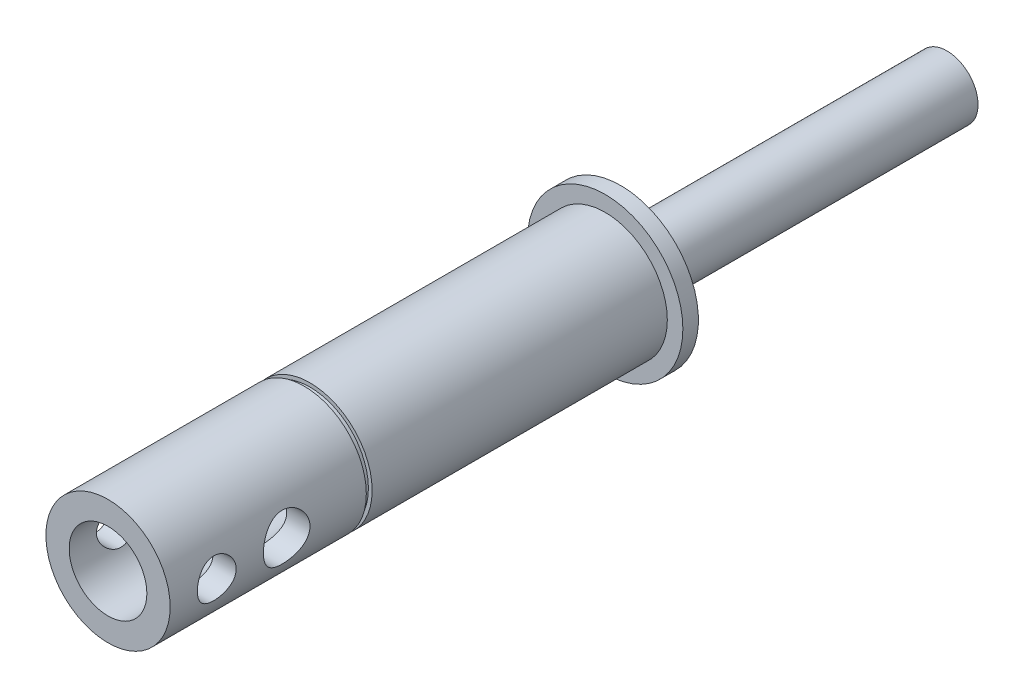
SolidWorks part; units mm, degrees
other "Markup1"
sketch "Sketch20" plane through (-15.875, -15.875, 171.45) normal (-1, 0, 0) x (0, 0, -1)
sketch "Sketch21" plane through (-15.875, -15.875, 171.45) normal (-1, 0, 0) x (0, 0, -1)
material "6061 Alloy"
ref_plane "Front Plane" through (0, 0, 0) normal (0, 0, 1) x (1, 0, 0)
ref_plane "Top Plane" through (0, 0, 0) normal (0, 1, 0) x (1, 0, 0)
ref_plane "Right Plane" through (0, 0, 0) normal (1, 0, 0) x (0, 0, -1)
sketch "Sketch1" plane through (0, 0, 0) normal (0, 0, 1) x (1, 0, 0)
  circle A0 centre (0, 0) radius 15.875
  dimension "D1" = 31.75
extrude "RawStock" add sketch "Sketch1" along normal blind 194.6402
sketch "Sketch10" plane through (0, 0, 194.6402) normal (0, 0, 1) x (1, 0, 0)
  circle A0 centre (0, 0) radius 12.7
extrude "FacingOp" cut sketch "Sketch10" against normal blind 23.1902
hole_wizard "ReliefHole" positions "Sketch2" profile "Sketch3" legacy
sketch "Sketch2" plane through (0, 0, 194.6402) normal (0, 0, 1) x (1, 0, 0)
  point P0 (0, 0)
sketch "Sketch3" plane through (0, 0, 194.6402) normal (1, 0, 0) x (0, -1, 0)
  line L0 (0, 0) -> (0, 95.8905)
  line L1 (0, 95.8905) -> (6.35, 92.075)
  line L2 (6.35, 92.075) -> (6.35, 0)
  line L4 (6.35, 0) -> (0, 0)
  line L6 (0, 95.8905) -> (-6.35, 92.075) construction
  line L7 (0, -4.2442) -> (0, 117.3081) construction
  dimension "Diameter" = 12.7
  dimension "Depth" = 92.075
  dimension "Drill Angle" = 118
hole_wizard "WiresHole" positions "Sketch4" profile "Sketch5" legacy
sketch "Sketch4" plane through (0, 0, 194.6402) normal (0, 0, 1) x (1, 0, 0)
  point P0 (0, 0)
sketch "Sketch5" plane through (0, 0, 194.6402) normal (1, 0, 0) x (0, -1, 0)
  line L0 (0, 0) -> (0, 120.0345)
  line L1 (0, 120.0345) -> (7.9375, 115.2652)
  line L2 (7.9375, 115.2652) -> (7.9375, 0)
  line L4 (7.9375, 0) -> (0, 0)
  line L6 (0, 120.0345) -> (-7.9375, 115.2652) construction
  line L7 (0, -4.2442) -> (0, 117.3081) construction
  dimension "Diameter" = 15.875
  dimension "Depth" = 115.2652
  dimension "Drill Angle" = 118
sketch "Sketch6" plane through (0, 0, 194.6402) normal (0, 0, 1) x (1, 0, 0)
  circle A0 centre (0, 0) radius 12.7
  dimension "D1" = 25.4
extrude "ShaftDiam" cut sketch "Sketch6" against normal blind 124.7902 flip side to cut
ref_plane "GroovePlane" through (0, 0, 130.175) normal (0, 0, 1) x (1, 0, 0)
sketch "Sketch7" plane through (0, 0, 130.175) normal (0, 0, 1) x (1, 0, 0)
  circle A0 centre (0, 0) radius 11.938
  dimension "D1" = 23.876
extrude "Groove" cut sketch "Sketch7" along normal blind 1.1906 flip side to cut
sketch "Sketch8" plane through (0, 0, 0) normal (0, 0, -1) x (-1, 0, 0)
  circle A0 centre (0, 0) radius 6.35
  dimension "D1" = 12.7
extrude "EncoderShaft" cut sketch "Sketch8" against normal blind 66.675 flip side to cut
ref_plane "Plane2" through (-12.7, 0, 0) normal (-1, 0, 0) x (0, 1, 0)
sketch "Sketch12" plane through (-12.7, 0, 0) normal (-1, 0, 0) x (0, 1, 0)
  line L0 (-12.7, -171.45) -> (12.7, -171.45) construction
  line L1 (0, -194.6402) -> (0, -74.6057) construction
  line L2 (-7.9375, -171.45) -> (7.9375, -171.45) construction
  circle A0 centre (0, -161.925) radius 3.9687
  circle A1 centre (0, -147.6375) radius 4.7625
  dimension "D1" = 7.9375
  dimension "D3" = 9.525
  dimension "D2" = 9.525
  dimension "D4" = 23.8125
extrude "Holes_Top" cut sketch "Sketch12" against normal through all
ref_plane "Plane1" through (0, -11.938, 0) normal (0, -1, 0) x (-1, 0, 0)
hole_wizard "SlipRingHole" positions "Sketch18" profile "Sketch19" legacy
sketch "Sketch18" plane through (0, 0, 66.675) normal (0, 0, -1) x (-1, 0, 0)
  line L0 (0, 17.4625) -> (0, -17.4625) construction
  circle A0 centre (0, 0) radius 8.7312 construction
  point P0 (0, -8.7312)
  dimension "D1" = 17.4625
sketch "Sketch19" plane through (0, -8.7312, 66.675) normal (1, 0, 0) x (0, 1, 0)
  line L0 (0, 0) -> (0, 26.8308)
  line L1 (0, 26.8308) -> (2.3812, 25.4)
  line L2 (2.3812, 25.4) -> (2.3812, 0)
  line L4 (2.3812, 0) -> (0, 0)
  line L6 (0, 26.8308) -> (-2.3812, 25.4) construction
  line L7 (0, -4.2442) -> (0, 117.3081) construction
  dimension "Diameter" = 4.7625
  dimension "Depth" = 25.4
  dimension "Drill Angle" = 118
